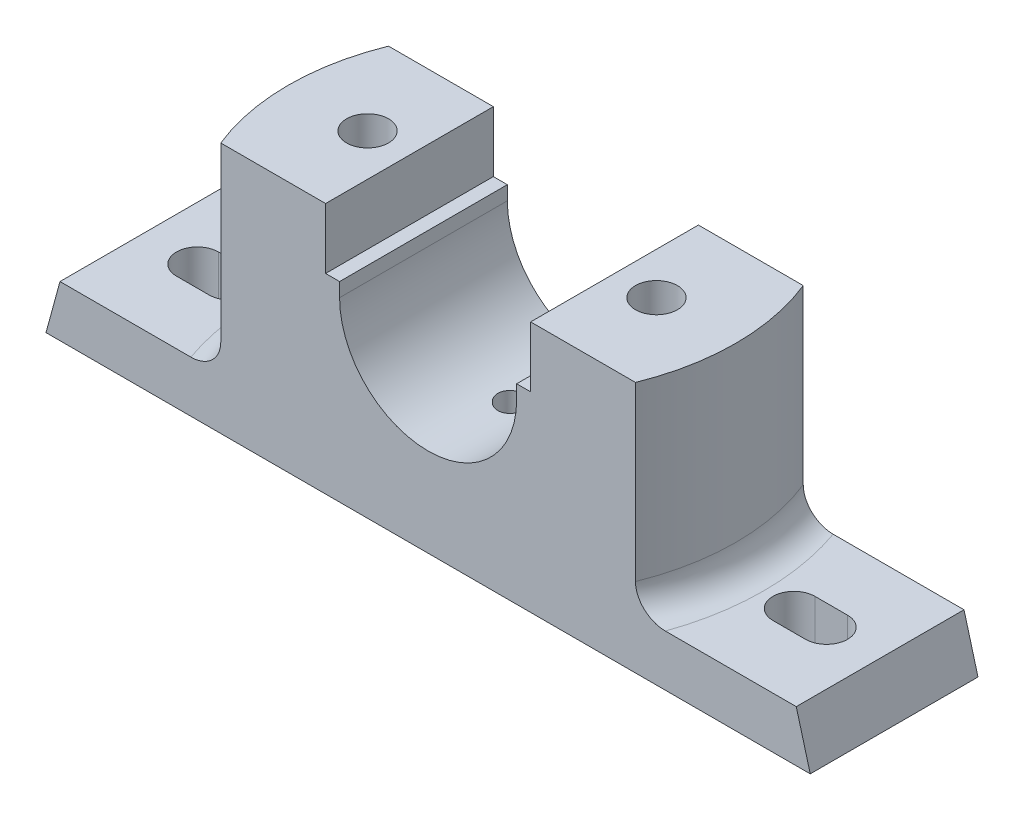
SolidWorks part; units mm, degrees
ref_plane "Front" through (0, 0, 0) normal (0, 0, 1) x (1, 0, 0)
ref_plane "Top" through (0, 0, 0) normal (0, 1, 0) x (1, 0, 0)
ref_plane "Right" through (0, 0, 0) normal (1, 0, 0) x (0, 0, -1)
sketch "Sketch1" plane through (0, 0, 0) normal (0, 0, 1) x (1, 0, 0)
  line L0 (-44.3372, 0) -> (57.8223, 0) construction
  line L1 (-19, 3) -> (-22, 3)
  line L2 (-22, 3) -> (-22, 16)
  line L3 (-22, 16) -> (-50, 16)
  line L4 (-50, 16) -> (-50, -27)
  line L5 (0, 48.9344) -> (0, -83.4643) construction
  line L6 (19, 3) -> (22, 3)
  line L7 (22, 3) -> (22, 16)
  line L8 (22, 16) -> (50, 16)
  line L9 (50, 16) -> (50, -27)
  line L10 (-50, -27) -> (-79, -27)
  line L11 (-79, -27) -> (-82, -38)
  line L12 (79, -27) -> (82, -38)
  line L13 (50, -27) -> (79, -27)
  line L14 (-82, -38) -> (82, -38)
  line L15 (-19, 3) -> (-19, 0)
  line L16 (19, 3) -> (19, 0)
  arc A0 (-19, 0) -> (19, 0) centre (0, 0) ccw
  dimension "D1" = 13
  dimension "D3" = 19
  dimension "D2" = 16
  dimension "D4" = 44
  dimension "D5" = 164
  dimension "D6" = 11
  dimension "D7" = 3
  dimension "D8" = 50
  dimension "D9" = 54
  dimension "D10" = 38
  dimension "D11" = 3
  dimension "D12" = 3
extrude "Boss-Extrude1" add sketch "Sketch1" along normal mid plane 36
sketch "Sketch2" plane through (0, 16, 0) normal (0, 1, 0) x (1, 0, 0)
  line L0 (-22, 18) -> (-50, 18) construction
  line L1 (-50, -18) -> (-50, 18) construction
  line L2 (-22, -18) -> (-50, -18) construction
  line L3 (-44.4972, 18) -> (-50, 18)
  line L4 (-50, -18) -> (-50, 18)
  line L5 (-44.4972, -18) -> (-50, -18)
  arc A0 (-44.4972, 18) -> (-44.4972, -18) centre (0, 0) ccw
  dimension "D1" = 48
extrude "Cut-Extrude1" cut sketch "Sketch2" against normal up to surface (43 mm away) up to face at (-64.5, -27, 0)
mirror "Mirror1" about plane through (0, 0, 0) normal (1, 0, 0) of "Cut-Extrude1"
sketch "Sketch3" plane through (0, -27, 0) normal (0, 1, 0) x (1, 0, 0)
  line L0 (-67.5, 0) -> (-60.5, 0) construction
  line L1 (-67.5, 4.5) -> (-60.5, 4.5)
  line L2 (-67.5, -4.5) -> (-60.5, -4.5)
  arc A0 (-67.5, 4.5) -> (-67.5, -4.5) centre (-67.5, 0) ccw
  arc A1 (-60.5, -4.5) -> (-60.5, 4.5) centre (-60.5, 0) ccw
  point P2 (-64, 0)
  dimension "D1" = 64
  dimension "D2" = 7
extrude "Cut-Extrude2" cut sketch "Sketch3" against normal through all
mirror "Mirror2" about plane through (0, 0, 0) normal (1, 0, 0) of "Cut-Extrude2"
sketch "Sketch4" plane through (0, 16, 0) normal (0, 1, 0) x (1, 0, 0)
  circle A0 centre (-31, 0) radius 4.5
  dimension "D1" = 9
  dimension "D2" = 31
extrude "Cut-Extrude3" cut sketch "Sketch4" against normal through all
mirror "Mirror3" about plane through (0, 0, 0) normal (1, 0, 0) of "Cut-Extrude3"
fillet "Fillet1" radius 6 2 edges at (48, -27, 0) (-48, -27, 0)
sketch "Sketch7" plane through (0, -38, 0) normal (0, -1, 0) x (1, 0, 0)
  line L1 (21, 10) -> (41, 10)
  line L2 (21, 10) -> (21, -10)
  line L3 (21, -10) -> (41, -10)
  line L4 (41, 10) -> (41, -10)
  line L5 (21, 10) -> (41, -10) construction
  line L6 (21, -10) -> (41, 10) construction
  point P0 (31, 0)
  dimension "D1" = 20
  dimension "D2" = 20
extrude "Cut-Extrude4" cut sketch "Sketch7" against normal blind 8
mirror "Mirror4" about plane through (0, 0, 0) normal (1, 0, 0) of "Cut-Extrude4"
hole_wizard "Ø6.0mm Dowel Hole2" positions "3DSketch10" profile "Sketch18" hole size "Ø6.0" standard "ANSI Metric"
sketch3d "3DSketch10"
  point P0 (0, -19, 0)
  dimension "D1" = 0
sketch "Sketch18" plane through (0, -19, 0) normal (1, 0, 0) x (0, 0, 1)
  line L0 (0, 0) -> (0, 7.8026)
  line L1 (0, 7.8026) -> (3, 6)
  line L2 (3, 6) -> (3, 0)
  line L5 (3, 0) -> (0, 0)
  line L10 (0, 7.8026) -> (-3, 6) construction
  line L11 (0, -6.35) -> (0, 107.95) construction
  dimension "Hole Dia." = 6
  dimension "Hole Depth" = 6
  dimension "Drill Angle" = 118
